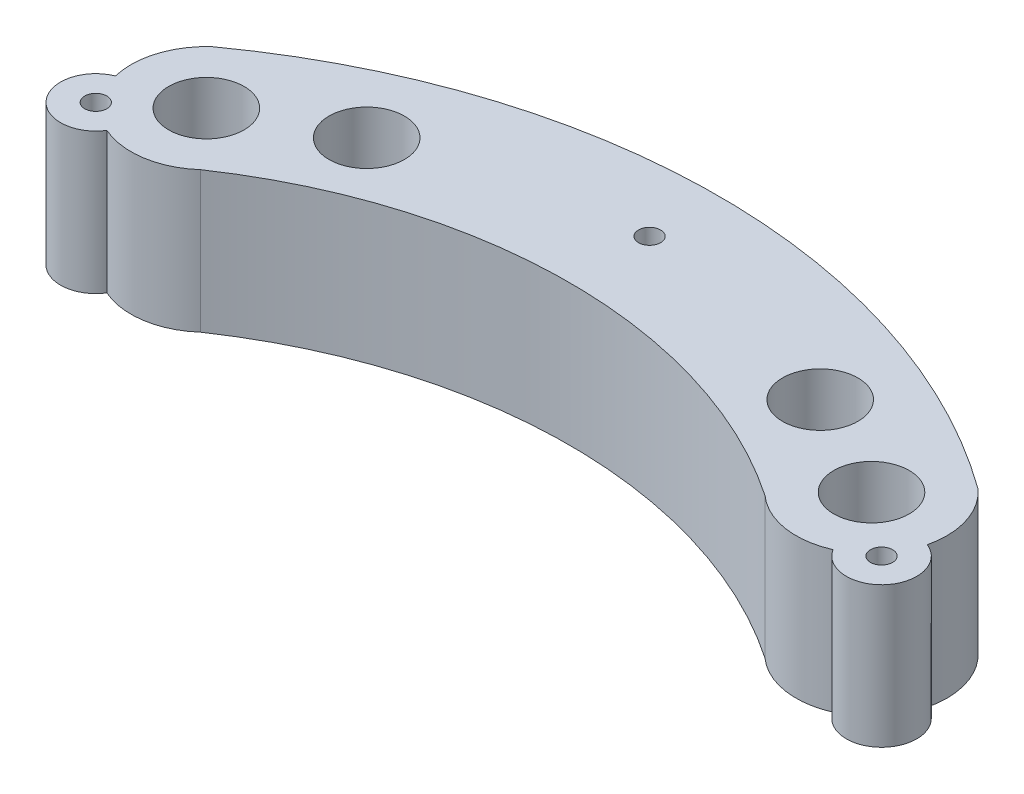
SolidWorks part; units mm, degrees
ref_plane "Front Plane" through (0, 0, 0) normal (0, 0, 1) x (1, 0, 0)
ref_plane "Top Plane" through (0, 0, 0) normal (0, 1, 0) x (1, 0, 0)
ref_plane "Right Plane" through (0, 0, 0) normal (1, 0, 0) x (0, 0, -1)
sketch "Sketch1" plane through (0, 0, 0) normal (0, 1, 0) x (1, 0, 0)
  circle A0 centre (0, 0) radius 4.7625
  circle A1 centre (13.3674, 6.8861) radius 4.7625
  circle A2 centre (70.647, 6.8861) radius 4.7625
  circle A3 centre (84.0144, 0) radius 4.7625
  dimension "D1" = 6.8861
  dimension "D2" = 13.3674
  dimension "D3" = 57.2796
  dimension "D4" = 13.3674
  dimension "D5" = 6.8861
  dimension "D6" = 0
  dimension "D8" = 9.525
  dimension "D9" = 9.525
  dimension "D10" = 9.525
  dimension "D11" = 9.525
  dimension "D7" = 0
sketch "Sketch2" plane through (0, 0, 0) normal (0, 1, 0) x (1, 0, 0)
  circle A0 centre (0, 0) radius 9.525
  circle A1 centre (84.0144, 0) radius 9.525
  arc A2 (-6.35, 7.0995) -> (90.3644, 7.0995) centre (42.0072, -59.804) cw
  arc A3 (6.35, -7.0995) -> (77.6644, -7.0995) centre (42.0072, -59.643) cw
  dimension "D1" = 19.05
  dimension "D2" = 19.05
  dimension "D4" = 82.55
  dimension "D5" = 63.5
  dimension "D3" = 0
  dimension "D6" = 6.35
  dimension "D7" = 6.35
  dimension "D8" = 6.35
extrude "Boss-Extrude1" add sketch "Sketch2" along normal blind 14.605 and the other way blind 3.175 contours A0 A3 | A0 A3 A1 A2 | A1 A3
extrude "Cut-Extrude1" cut sketch "Sketch1" along normal blind 20.32
sketch "Sketch4" plane through (0, 0, 0) normal (0, 1, 0) x (1, 0, 0)
  circle A0 centre (13.3674, 6.8861) radius 2.2225
  circle A1 centre (0, 0) radius 2.2225
  circle A2 centre (70.647, 6.8861) radius 2.2225
  circle A3 centre (84.0144, 0) radius 2.2225
  dimension "D1" = 4.445
  dimension "D2" = 4.445
  dimension "D3" = 4.445
  dimension "D4" = 4.445
extrude "Cut-Extrude2" cut sketch "Sketch4" against normal blind 20.32
sketch "Sketch5" plane through (0, 14.605, 0) normal (0, 1, 0) x (1, 0, 0)
  circle A0 centre (-7.62, -6.35) radius 4.445
  circle A1 centre (91.6344, -6.35) radius 4.445
  circle A2 centre (84.0144, 0) radius 4.7625 construction
  dimension "D1" = 8.89
  dimension "D2" = 8.89
  dimension "D3" = 6.35
  dimension "D4" = 7.62
  dimension "D5" = 7.62
  dimension "D6" = 6.35
extrude "Boss-Extrude2" add sketch "Sketch5" against normal blind 17.78
sketch "Sketch6" plane through (0, 14.605, 0) normal (0, 1, 0) x (1, 0, 0)
  circle A0 centre (42.0072, 13.97) radius 1.397
  circle A1 centre (-7.62, -6.35) radius 1.397
  circle A2 centre (91.6344, -6.35) radius 1.397
  arc A4 (90.3644, 7.0995) -> (-6.35, 7.0995) centre (42.0072, -59.804) ccw construction
  dimension "D1" = 2.794
  dimension "D2" = 2.794
  dimension "D3" = 2.794
  dimension "D4" = 0
  dimension "D5" = 20.32
extrude "Cut-Extrude3" cut sketch "Sketch6" against normal blind 17.78
